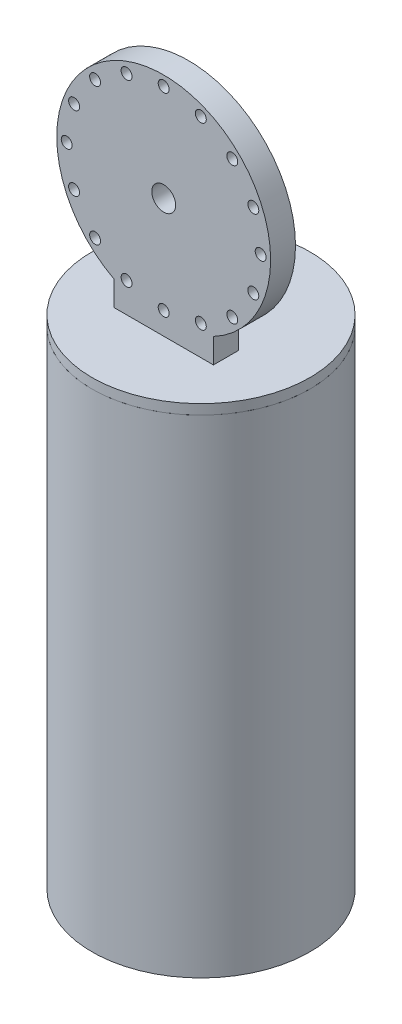
SolidWorks part; units mm, degrees
ref_plane "Plano frontal" through (0, 0, 0) normal (0, 0, 1) x (1, 0, 0)
ref_plane "Plano superior" through (0, 0, 0) normal (0, 1, 0) x (1, 0, 0)
ref_plane "Plano direito" through (0, 0, 0) normal (1, 0, 0) x (0, 0, -1)
sketch "Esboço1" plane through (0, 0, 0) normal (0, 0, 1) x (1, 0, 0)
  line L0 (0, 0) -> (0, 490) construction
  line L1 (0, 0) -> (215.8131, 0) construction
  line L2 (105.78, 490) -> (109.54, 490)
  line L4 (105.78, 0) -> (109.54, 0)
  line L7 (105.78, 0) -> (105.78, 490)
  line L11 (109.54, 490) -> (109.54, 0)
  dimension "D1" = 3.76
  dimension "D6" = 490
  dimension "D7" = 219.08
revolve "Revolução1" add sketch "Esboço1" angle 360 about L0
sketch "Esboço3" plane through (0, 490, 0) normal (0, 1, 0) x (1, 0, 0)
  circle A1 centre (0, 0) radius 109.54 construction
  circle A2 centre (0, 0) radius 109.54
extrude "Ressalto-extrusão1" add sketch "Esboço3" along normal blind 10 separate body
sketch "Esboço4" plane through (0, 0, 0) normal (0, 0, 1) x (1, 0, 0)
  line L0 (0, 500) -> (0, 792.0043) construction
  line L2 (-50, 500) -> (-50, 524.8357)
  line L3 (-50, 500) -> (50, 500)
  line L4 (50, 500) -> (50, 524.8357)
  line L5 (109.54, 500) -> (-109.54, 500) construction
  circle A0 centre (0, 620) radius 97.5 construction
  circle A1 centre (0, 620) radius 12
  arc A2 (50, 524.8357) -> (-50, 524.8357) centre (0, 620) ccw
  circle A3 centre (0, 717.5) radius 5.5
  circle A4 centre (37.3116, 710.0783) radius 5.5
  circle A5 centre (68.9429, 688.9429) radius 5.5
  circle A6 centre (90.0783, 657.3116) radius 5.5
  circle A7 centre (97.5, 620) radius 5.5
  circle A8 centre (90.0783, 582.6884) radius 5.5
  circle A9 centre (68.9429, 551.0571) radius 5.5
  circle A10 centre (37.3116, 529.9217) radius 5.5
  circle A11 centre (0, 522.5) radius 5.5
  circle A12 centre (-37.3116, 529.9217) radius 5.5
  circle A13 centre (-68.9429, 551.0571) radius 5.5
  circle A14 centre (-90.0783, 582.6884) radius 5.5
  circle A15 centre (-97.5, 620) radius 5.5
  circle A16 centre (-90.0783, 657.3116) radius 5.5
  circle A17 centre (-68.9429, 688.9429) radius 5.5
  circle A18 centre (-37.3116, 710.0783) radius 5.5
  point P46 (0, 620)
  dimension "D1" = 24
  dimension "D4" = 215
  dimension "D5" = 195
  dimension "D6" = 11
  dimension "D2" = 120
  dimension "D3" = 100
  dimension "D7" = 16
extrude "Ressalto-extrusão2" add sketch "Esboço4" along normal blind 25 from offset 12.5
